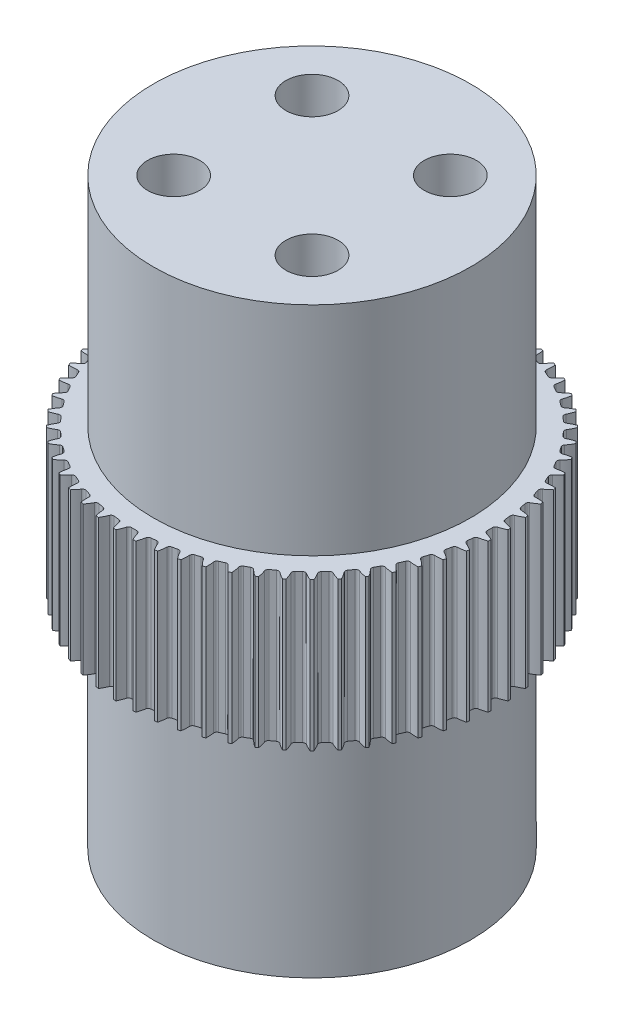
SolidWorks part; units mm, degrees
ref_plane "Front Plane" through (0, 0, 0) normal (0, 0, 1) x (1, 0, 0)
ref_plane "Top Plane" through (0, 0, 0) normal (0, 1, 0) x (1, 0, 0)
ref_plane "Right Plane" through (0, 0, 0) normal (1, 0, 0) x (0, 0, -1)
sketch "Sketch1" plane through (0, 0, 0) normal (0, 1, 0) x (1, 0, 0)
  circle A0 centre (0, 0) radius 19
extrude "Boss-Extrude1" add sketch "Sketch1" along normal blind 15
sketch "Sketch2" plane through (0, 15, 0) normal (0, 1, 0) x (1, 0, 0)
  line L0 (-0.2687, 18) -> (0.2687, 18)
  arc A1 (0.2687, 18) -> (0.5569, 18.2167) centre (0.2687, 18.3) ccw
  circle A2 centre (0, 0) radius 8
  arc A3 (0.5569, 18.2167) -> (1, 19.25) centre (4.9375, 16.95) cw
  arc A4 (-0.5569, 18.2167) -> (-1, 19.25) centre (-4.9375, 16.95) ccw
  arc A5 (-1, 19.25) -> (1, 19.25) centre (0, 16.031) cw
  arc A6 (-0.5569, 18.2167) -> (-0.2687, 18) centre (-0.2687, 18.3) ccw
  point P12 (0.5, 18)
  dimension "D1" = 3.3708
  dimension "D4" = 4.56
  dimension "D5" = 0.3
  dimension "D2" = 0.5
  dimension "D3" = 1.25
extrude "Cut-Extrude1" cut sketch "Sketch2" against normal through all
pattern_circular "CirPattern1" count 60 over 360 about axis through (0, 0, 0) along (0, 1, 0) of "Cut-Extrude1"
sketch "Sketch3" plane through (0, 15, 0) normal (0, 1, 0) x (1, 0, 0)
  circle A0 centre (0, 0) radius 8
extrude "Boss-Extrude2" add sketch "Sketch3" against normal blind 15
sketch "Sketch4" plane through (0, 15, 0) normal (0, 1, 0) x (1, 0, 0)
  circle A0 centre (0, 0) radius 16.05
extrude "Boss-Extrude3" add sketch "Sketch4" along normal blind 22
sketch "Sketch5" plane through (0, 0, 0) normal (0, -1, 0) x (1, 0, 0)
  circle A1 centre (0, 0) radius 16.05
extrude "Boss-Extrude4" add sketch "Sketch5" along normal blind 22
sketch "Sketch6" plane through (0, -22, 0) normal (0, -1, 0) x (1, 0, 0)
  line L1 (-7, -7) -> (7, -7)
  line L2 (-7, -7) -> (-7, 7)
  line L3 (-7, 7) -> (7, 7)
  line L4 (7, -7) -> (7, 7)
  line L5 (-7, -7) -> (7, 7) construction
  line L6 (-7, 7) -> (7, -7) construction
  circle A0 centre (0, 0) radius 1.5002
  circle A1 centre (-7, 7) radius 2.64
  circle A2 centre (7, 7) radius 2.64
  circle A3 centre (7, -7) radius 2.64
  circle A4 centre (-7, -7) radius 2.64
  dimension "D1" = 14
  dimension "D2" = 14
extrude "Cut-Extrude2" cut sketch "Sketch6" against normal blind 125 contours L3 A1 L2 | L2 A1 L3 | L4 A2 L3 | L1 A3 L4 | L2 A4 L1 | L1 A4 L2 | L4 A3 L1 | L3 A2 L4
